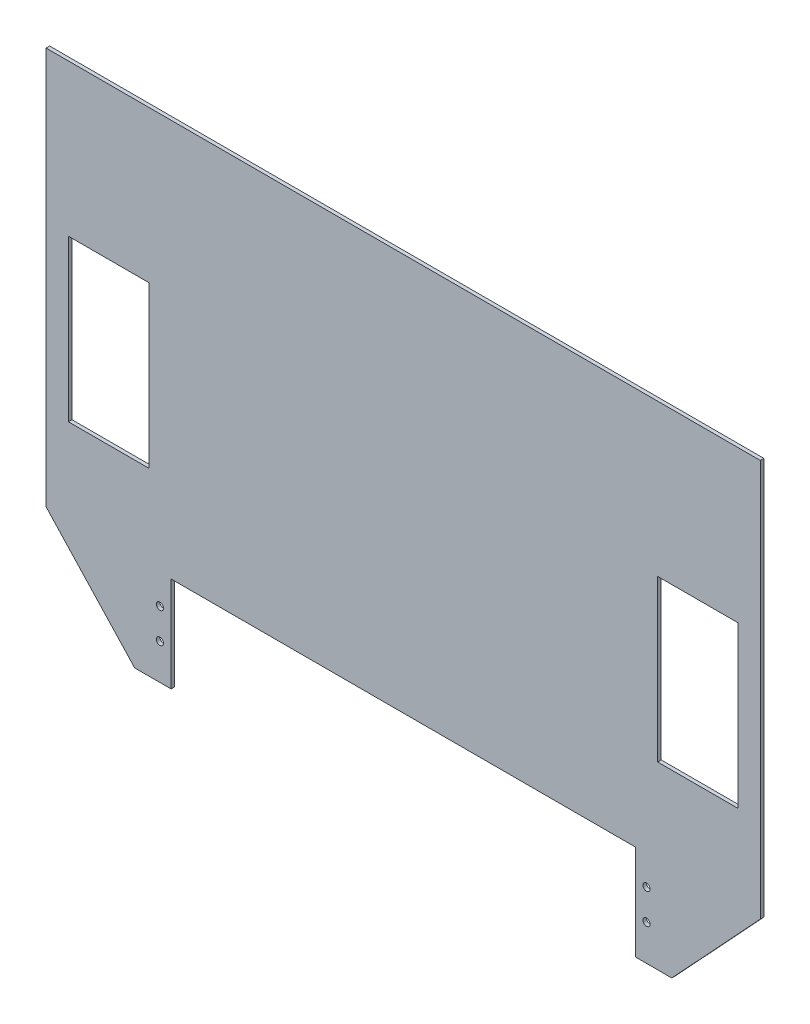
SolidWorks part; units mm, degrees
material "6061-T6 (SS)"
ref_plane "Front Plane" through (0, 0, 0) normal (0, 0, 1) x (1, 0, 0)
ref_plane "Top Plane" through (0, 0, 0) normal (0, 1, 0) x (1, 0, 0)
ref_plane "Right Plane" through (0, 0, 0) normal (1, 0, 0) x (0, 0, -1)
sketch "Sketch1" plane through (0, 0, 0) normal (0, 0, 1) x (1, 0, 0)
  line L0 (0, 0) -> (0, -179.6341) construction
  line L1 (200, 0) -> (-200, 0)
  line L2 (-200, 0) -> (-200, -222.5)
  line L3 (-200, -222.5) -> (-150.4043, -275.82)
  line L4 (-150.4043, -275.82) -> (-130, -275.82)
  line L5 (-130, -275.82) -> (-130, -222.5)
  line L6 (-130, -222.5) -> (130, -222.5)
  line L7 (130, -275.82) -> (130, -222.5)
  line L8 (150.4043, -275.82) -> (130, -275.82)
  line L9 (200, -222.5) -> (150.4043, -275.82)
  line L10 (200, 0) -> (200, -222.5)
  line L11 (187.5, -85) -> (142.5, -175) construction
  line L12 (-187.5, -85) -> (-142.5, -85)
  line L13 (-187.5, -85) -> (-187.5, -175)
  line L14 (-187.5, -175) -> (-142.5, -175)
  line L15 (-142.5, -85) -> (-142.5, -175)
  line L16 (-187.5, -85) -> (-142.5, -175) construction
  line L17 (-187.5, -175) -> (-142.5, -85) construction
  line L18 (187.5, -175) -> (142.5, -85) construction
  line L19 (187.5, -85) -> (187.5, -175)
  line L20 (187.5, -175) -> (142.5, -175)
  line L21 (142.5, -85) -> (142.5, -175)
  line L22 (187.5, -85) -> (142.5, -85)
  point P10 (0, -222.5)
  point P14 (-165, -130)
  dimension "D1" = 200
  dimension "D2" = 222.5
  dimension "D3" = 72.82
  dimension "D4" = 130
  dimension "D6" = 222.5
  dimension "D7" = 90
  dimension "D8" = 45
  dimension "D9" = 12.5
  dimension "D10" = 130
  dimension "D11" = 53.32
extrude "Boss-Extrude1" add sketch "Sketch1" along normal blind 2
sketch "Sketch2" plane through (0, 0, 2) normal (0, 0, 1) x (1, 0, 0)
  line L0 (-130, -275.82) -> (-130, -222.5) construction
  line L1 (-150.4043, -275.82) -> (-130, -275.82) construction
  line L2 (0, 0) -> (0, -251.7691) construction
  circle A0 centre (-136.25, -238.82) radius 2
  circle A1 centre (-136.25, -255.82) radius 2
  circle A2 centre (136.25, -255.82) radius 2
  circle A3 centre (136.25, -238.82) radius 2
  dimension "D4" = 4
  dimension "D5" = 4
  dimension "D1" = 6.25
  dimension "D2" = 20
  dimension "D3" = 17
extrude "Cut-Extrude1" cut sketch "Sketch2" against normal blind 10
